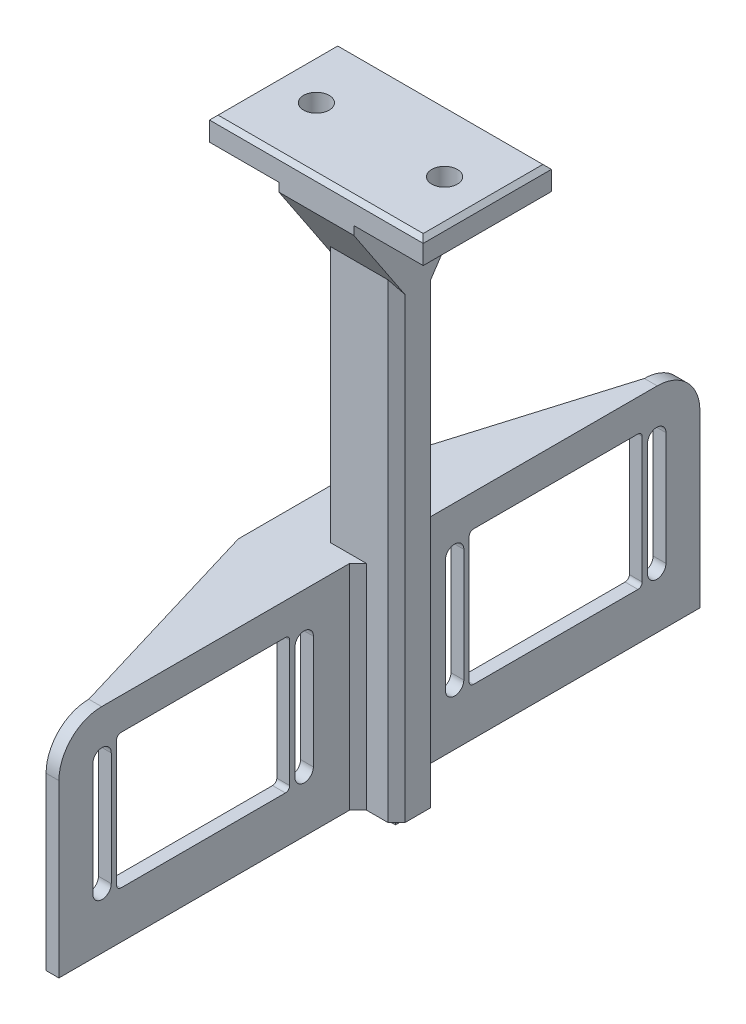
SolidWorks part; units mm, degrees
ref_plane "前视基准面" through (0, 0, 0) normal (0, 0, 1) x (1, 0, 0)
ref_plane "上视基准面" through (0, 0, 0) normal (0, 1, 0) x (1, 0, 0)
ref_plane "右视基准面" through (0, 0, 0) normal (1, 0, 0) x (0, 0, -1)
sketch "草图2" plane through (0, 0, 0) normal (0, 1, 0) x (1, 0, 0)
  line L1 (0, 0) -> (17.5, 0)
  line L2 (0, 0) -> (0, 10)
  line L3 (0, 10) -> (17.5, 10)
  line L4 (17.5, 0) -> (17.5, 10)
  dimension "D1" = 17.5
  dimension "D2" = 10
extrude "凸台-拉伸1" add sketch "草图2" along normal blind 125
sketch "草图3" plane through (0, 125, 0) normal (0, 1, 0) x (1, 0, 0)
  line L0 (0, 10) -> (0, 0) construction
  line L1 (-16.25, 20) -> (33.75, 20)
  line L2 (-16.25, 20) -> (-16.25, -10)
  line L3 (-16.25, -10) -> (33.75, -10)
  line L4 (33.75, 20) -> (33.75, -10)
  line L5 (0, 0) -> (17.5, 0) construction
  line L10 (0, 10) -> (0, 0)
  line L11 (0, 0) -> (17.5, 0)
  line L12 (17.5, 0) -> (17.5, 10)
  line L13 (17.5, 10) -> (0, 10)
  line L15 (0, 0) -> (0.4167, 0)
  point P0 (8.75, 5)
  dimension "D1" = 50
  dimension "D2" = 30
  dimension "D3" = 0
  dimension "D4" = 0.4167
  dimension "D5" = 8.75
  dimension "D6" = 33.75
  dimension "D7" = 5
  dimension "D8" = 20
extrude "凸台-拉伸2" add sketch "草图3" along normal blind 7.5 contours L3 L4 L1 L2
chamfer "倒角1" distance 1 angle 45 4 edges at (8.75, 132.5, -20) (-16.25, 132.5, -5) (8.75, 132.5, 10) (33.75, 132.5, -5)
sketch "草图4" plane through (0, 132.5, 0) normal (0, 1, 0) x (1, 0, 0)
  circle A0 centre (23.75, 5) radius 3
  circle A1 centre (-6.25, 5) radius 3
extrude "切除-拉伸1" cut sketch "草图4" against normal blind 10
sketch "草图5" plane through (17.5, 0, 0) normal (1, 0, 0) x (0, 0, -1)
  line L0 (10, 125) -> (20, 125)
  line L1 (20, 125) -> (10, 110)
  line L2 (10, 125) -> (10, 0) construction
  line L3 (10, 110) -> (10, 125)
  line L4 (0, 125) -> (-10, 125)
  line L5 (-10, 125) -> (0, 110)
  line L6 (0, 125) -> (0, 0) construction
  line L7 (0, 110) -> (0, 125)
  dimension "D1" = 15
  dimension "D2" = 15
extrude "凸台-拉伸3" add sketch "草图5" against normal blind 17.5
chamfer "倒角2" distance 2 angle 45 6 edges at (25.625, 125, -20) (33.75, 125, -5) (25.625, 125, 10) (-8.125, 125, -20) (-8.125, 125, 10) (-16.25, 125, -5)
chamfer "倒角3" distance 2 angle 45 4 edges at (17.5, 55, 0) (17.5, 55, -10) (0, 55, -10) (0, 55, 0)
sketch "草图6" plane through (0, 0, 0) normal (0, -1, 0) x (1, 0, 0)
  line L1 (3.75, -3.5) -> (13.75, -3.5)
  line L2 (3.75, -3.5) -> (3.75, -6.5)
  line L3 (3.75, -6.5) -> (13.75, -6.5)
  line L4 (13.75, -3.5) -> (13.75, -6.5)
  line L5 (3.75, -3.5) -> (13.75, -6.5) construction
  line L6 (3.75, -6.5) -> (13.75, -3.5) construction
  point P0 (8.75, -5)
  dimension "D1" = 10
  dimension "D2" = 3
extrude "凸台-拉伸4" add sketch "草图6" along normal blind 3.1
ref_plane "基准面4" through (8.75, 0, 0) normal (-1, 0, 0) x (0, 0, 1)
ref_plane "基准面5" through (0, 0, -5) normal (0, 0, -1) x (-1, 0, 0)
sketch "草图7" plane through (8.75, 0, 0) normal (-1, 0, 0) x (0, 0, 1)
  line L0 (-10, 0) -> (-80, 0)
  line L2 (-10, 0) -> (-10, 110) construction
  line L3 (-10, 50) -> (-10, 0)
  line L4 (-10, 50) -> (-80, 50)
  line L5 (-80, 50) -> (-80, 0)
  dimension "D1" = 70
  dimension "D2" = 50
extrude "凸台-拉伸5" add sketch "草图7" along normal blind 3.25 contours L0 L5 L4 L3
mirror "镜向1" about plane through (0, 0, -5) normal (0, 0, -1) of "凸台-拉伸5"
sketch "草图12" plane through (0, 0, -10) normal (0, 0, -1) x (-1, 0, 0)
  line L1 (-15.5, 0) -> (-20, 0)
  line L2 (-15.5, 0) -> (-15.5, 6)
  line L3 (-15.5, 6) -> (-20, 6)
  line L4 (-20, 0) -> (-20, 6)
  dimension "D1" = 4.5
  dimension "D2" = 6
extrude "凸台-拉伸6" add sketch "草图12" against normal blind 10
mirror "镜向2" about plane through (8.75, 0, 0) normal (-1, 0, 0) of "凸台-拉伸6"
sketch "草图13" plane through (0, 6, 0) normal (0, 1, 0) x (1, 0, 0)
  line L6 (17.5, 8) -> (17.5, 2)
  line L7 (17.5, 2) -> (15.5, 0)
  line L8 (15.5, 0) -> (20, 0)
  line L9 (20, 0) -> (20, 10)
  line L10 (20, 10) -> (15.5, 10)
  line L11 (15.5, 10) -> (17.5, 8)
  line L12 (17.5, 8) -> (17.5, 2)
  line L13 (17.5, 2) -> (15.5, 0)
  line L14 (15.5, 0) -> (20, 0)
  line L15 (20, 0) -> (20, 10)
  line L16 (20, 10) -> (15.5, 10)
  line L17 (15.5, 10) -> (17.5, 8)
  dimension "D1" = 0
extrude "切除-拉伸4" cut sketch "草图13" against normal blind 10
ref_plane "基准面7" through (0, 0, -5) normal (0, 0, 1) x (1, 0, 0)
sketch "草图15" plane through (8.75, 0, 0) normal (1, 0, 0) x (0, 0, -1)
  line L1 (-70, 50) -> (0, 50)
  line L2 (-70, 50) -> (-70, 0)
  line L3 (-70, 0) -> (0, 0)
  line L4 (0, 50) -> (0, 0)
  line L5 (10, 50) -> (80, 50)
  line L6 (10, 50) -> (10, 0)
  line L7 (10, 0) -> (80, 0)
  line L8 (80, 50) -> (80, 0)
extrude "切除-拉伸7" cut sketch "草图15" against normal blind 0.25
sketch "草图16" plane through (5.5, 0, 0) normal (-1, 0, 0) x (0, 0, 1)
  line L0 (-10, 6) -> (-10, 110) construction
  line L1 (-26, 42.5) -> (-66.5, 42.5)
  line L2 (-26, 42.5) -> (-26, 11)
  line L3 (-26, 11) -> (-66.5, 11)
  line L4 (-66.5, 42.5) -> (-66.5, 11)
  line L5 (-10, 0) -> (-80, 0) construction
  line L6 (-10, 50) -> (-80, 50) construction
  line L7 (-5, 0) -> (-5, 28.0891) construction
  line L9 (16, 11) -> (56.5, 11)
  line L10 (56.5, 42.5) -> (56.5, 11)
  line L11 (16, 42.5) -> (56.5, 42.5)
  line L12 (16, 42.5) -> (16, 11)
  dimension "D1" = 40.5
  dimension "D2" = 16
  dimension "D3" = 11
  dimension "D4" = 7.5
extrude "切除-拉伸8" cut sketch "草图16" against normal blind 39.25
chamfer "倒角7" distance 2 angle 45 4 edges at (8.5, 25, 0) (8.5, 25, -10) (5.5, 25, -10) (5.5, 25, 0)
fillet "圆角1" radius 1 8 edges at (7, 11, -66.5) (7, 11, -26) (7, 42.5, -26) (7, 42.5, -66.5) (7, 11, 56.5) (7, 42.5, 56.5) (7, 42.5, 16) (7, 11, 16)
fillet "圆角2" radius 10 2 edges at (7, 50, -80) (7, 50, 70)
sketch "草图17" plane through (0, 50, 0) normal (0, 1, 0) x (1, 0, 0)
  line L0 (5.5, 70) -> (-9.5, 20)
  line L1 (-16.25, 20) -> (33.75, 20) construction
  line L2 (-9.5, 20) -> (-9.5, -10)
  line L3 (33.75, -10) -> (-16.25, -10) construction
  line L4 (-9.5, -10) -> (5.5, -60)
  line L5 (5.5, 12) -> (5.5, 70) construction
  line L6 (5.5, 70) -> (5.5, -60)
  dimension "D1" = 15
extrude "凸台-拉伸7" add sketch "草图17" against normal blind 3
sketch "草图18" plane through (5.5, 0, 0) normal (-1, 0, 0) x (0, 0, 1)
  line L0 (59.9, 39.5) -> (59.9, 13) construction
  line L1 (62.05, 39.5) -> (62.05, 13)
  line L2 (57.75, 39.5) -> (57.75, 13)
  line L3 (56.5, 12) -> (56.5, 41.5) construction
  line L4 (55.5, 42.5) -> (17, 42.5) construction
  line L5 (17, 11) -> (55.5, 11) construction
  line L6 (36.25, 42.5) -> (36.25, 11) construction
  line L7 (-5, 6) -> (-5, 47) construction
  line L8 (0, 6) -> (-10, 6) construction
  line L9 (-8, 47) -> (-2, 47) construction
  line L10 (12.6, 39.5) -> (12.6, 13) construction
  line L11 (10.45, 39.5) -> (10.45, 13)
  line L12 (14.75, 39.5) -> (14.75, 13)
  line L13 (-22.6, 39.5) -> (-22.6, 13) construction
  line L14 (-20.45, 39.5) -> (-20.45, 13)
  line L15 (-24.75, 39.5) -> (-24.75, 13)
  line L16 (-69.9, 39.5) -> (-69.9, 13) construction
  line L17 (-72.05, 39.5) -> (-72.05, 13)
  line L18 (-67.75, 39.5) -> (-67.75, 13)
  arc A0 (62.05, 39.5) -> (57.75, 39.5) centre (59.9, 39.5) ccw
  arc A1 (57.75, 13) -> (62.05, 13) centre (59.9, 13) ccw
  arc A2 (10.45, 39.5) -> (14.75, 39.5) centre (12.6, 39.5) cw
  arc A3 (14.75, 13) -> (10.45, 13) centre (12.6, 13) cw
  arc A4 (-20.45, 39.5) -> (-24.75, 39.5) centre (-22.6, 39.5) ccw
  arc A5 (-24.75, 13) -> (-20.45, 13) centre (-22.6, 13) ccw
  arc A6 (-72.05, 39.5) -> (-67.75, 39.5) centre (-69.9, 39.5) cw
  arc A7 (-67.75, 13) -> (-72.05, 13) centre (-69.9, 13) cw
  point P2 (59.9, 26.25)
  point P23 (12.6, 26.25)
  point P30 (-22.6, 26.25)
  point P37 (-69.9, 26.25)
  dimension "D2" = 2.15
  dimension "D1" = 3.4
  dimension "D3" = 3
  dimension "D4" = 2
extrude "切除-拉伸9" cut sketch "草图18" against normal blind 48
